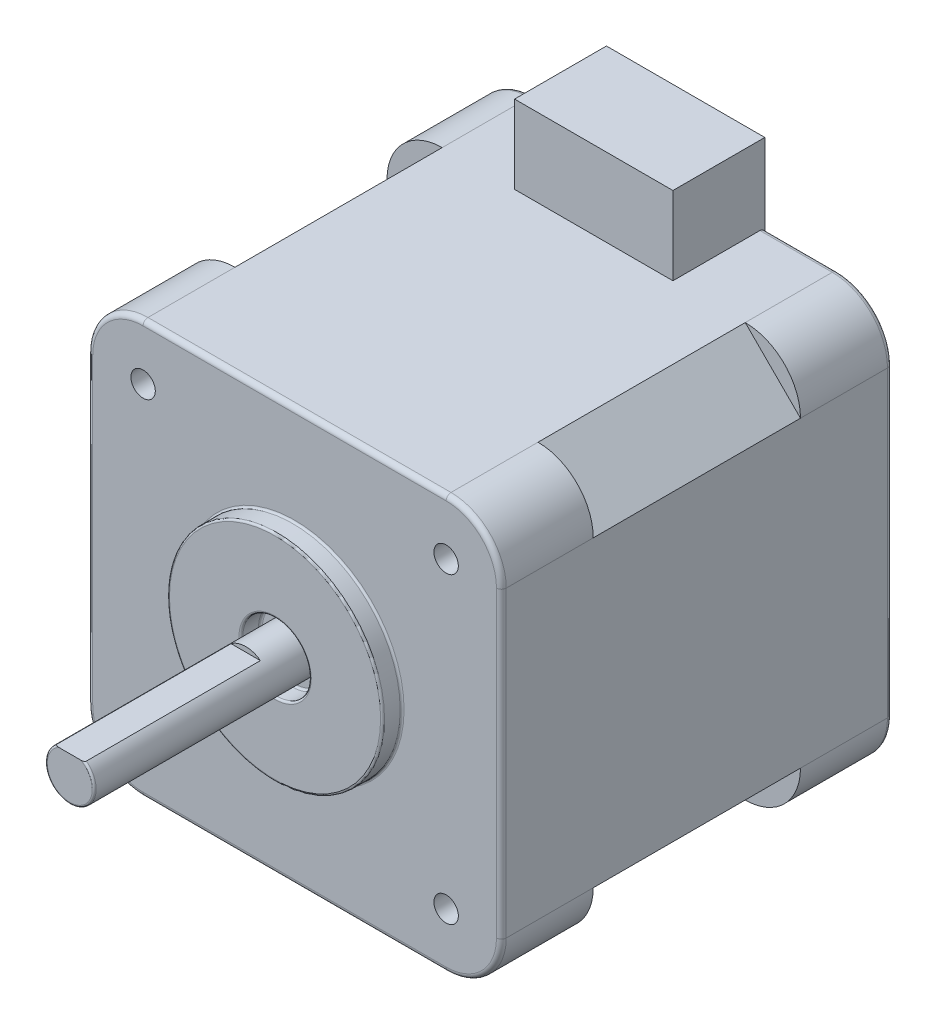
SolidWorks part; units mm, degrees
ref_plane "前视基准面" through (0, 0, 0) normal (0, 0, 1) x (1, 0, 0)
ref_plane "上视基准面" through (0, 0, 0) normal (0, 1, 0) x (1, 0, 0)
ref_plane "右视基准面" through (0, 0, 0) normal (1, 0, 0) x (0, 0, -1)
sketch "草图1" plane through (0, 0, 0) normal (0, 0, 1) x (1, 0, 0)
  line L1 (-21.15, -21.15) -> (21.15, -21.15)
  line L2 (-21.15, -21.15) -> (-21.15, 21.15)
  line L3 (-21.15, 21.15) -> (21.15, 21.15)
  line L4 (21.15, -21.15) -> (21.15, 21.15)
  line L5 (-21.15, -21.15) -> (21.15, 21.15) construction
  line L6 (-21.15, 21.15) -> (21.15, -21.15) construction
  point P0 (0, 0)
  dimension "D1" = 42.3
  dimension "D2" = 42.3
extrude "凸台-拉伸1" add sketch "草图1" along normal mid plane 21.2
chamfer "倒角1" distance 5.65 4 edges at (21.15, -21.15, 0) (-21.15, -21.15, 0) (-21.15, 21.15, 0) (21.15, 21.15, 0)
sketch "草图3" plane through (0, 0, 10.6) normal (0, 0, 1) x (1, 0, 0)
  line L0 (15.5, 21.15) -> (-15.5, 21.15) construction
  line L1 (21.15, -21.15) -> (-21.15, -21.15)
  line L2 (21.15, -21.15) -> (21.15, 21.15)
  line L3 (21.15, 21.15) -> (-21.15, 21.15)
  line L4 (-21.15, -21.15) -> (-21.15, 21.15)
  line L5 (21.15, -21.15) -> (-21.15, 21.15) construction
  line L6 (21.15, 21.15) -> (-21.15, -21.15) construction
  line L8 (-21.15, 15.5) -> (-21.15, -15.5) construction
  point P0 (0, 0)
extrude "凸台-拉伸2" add sketch "草图3" along normal blind 9.4
fillet "圆角1" radius 5.65 4 edges at (21.15, 21.15, 15.3) (21.15, -21.15, 15.3) (-21.15, -21.15, 15.3) (-21.15, 21.15, 15.3)
hole_wizard "M3 螺纹孔1" positions "草图4" profile "草图5" tap size "M3" standard "GB"
sketch "草图4" plane through (0, 0, 20) normal (0, 0, 1) x (1, 0, 0)
  point P0 (-15.5, -15.5)
  point P3 (15.5, -15.5)
  point P6 (15.5, 15.5)
  point P9 (-15.5, 15.5)
sketch "草图5" plane through (-15.5, -15.5, 20) normal (1, 0, 0) x (0, -1, 0)
  line L0 (0, 0) -> (0, 5.2511)
  line L1 (0, 5.2511) -> (1.25, 4.5)
  line L2 (1.25, 4.5) -> (1.25, 0)
  line L5 (1.25, 0) -> (0, 0)
  line L10 (0, 5.2511) -> (-1.25, 4.5) construction
  line L11 (0, -6.35) -> (0, 107.95) construction
  dimension "螺纹孔钻头直径" = 2.5
  dimension "螺纹孔钻头深度" = 4.5
  dimension "导头角度" = 118
cosmetic thread "孔螺蚊线1" parameters "D1"=4.5, "D2"=3
cosmetic thread "孔螺蚊线2" parameters "D1"=4.5, "D2"=3
cosmetic thread "孔螺蚊线3" parameters "D1"=4.5, "D2"=3
cosmetic thread "孔螺蚊线4" parameters "D1"=4.5, "D2"=3
sketch "草图6" plane through (0, 0, -10.6) normal (0, 0, -1) x (-1, 0, 0)
  line L1 (21.15, -21.15) -> (-21.15, -21.15)
  line L2 (21.15, -21.15) -> (21.15, 21.15)
  line L3 (21.15, 21.15) -> (-21.15, 21.15)
  line L4 (-21.15, -21.15) -> (-21.15, 21.15)
  line L5 (21.15, -21.15) -> (-21.15, 21.15) construction
  line L6 (21.15, 21.15) -> (-21.15, -21.15) construction
  line L7 (-15.5, 21.15) -> (15.5, 21.15) construction
  line L8 (-21.15, -15.5) -> (-21.15, 15.5) construction
  point P0 (0, 0)
extrude "凸台-拉伸3" add sketch "草图6" along normal blind 9.4
fillet "圆角2" radius 5.65 4 edges at (-21.15, -21.15, -15.3) (21.15, -21.15, -15.3) (21.15, 21.15, -15.3) (-21.15, 21.15, -15.3)
sketch "草图7" plane through (0, 21.15, 0) normal (0, 1, 0) x (1, 0, 0)
  line L0 (-15.5, 20) -> (15.5, 20) construction
  line L1 (8.1, 10.6) -> (-8.1, 10.6)
  line L2 (8.1, 10.6) -> (8.1, 20)
  line L3 (8.1, 20) -> (-8.1, 20)
  line L4 (-8.1, 10.6) -> (-8.1, 20)
  line L5 (8.1, 10.6) -> (-8.1, 20) construction
  line L6 (8.1, 20) -> (-8.1, 10.6) construction
  line L7 (15.5, 10.6) -> (21.15, 10.6) construction
  point P0 (0, 15.3)
  dimension "D1" = 16.2
extrude "凸台-拉伸4" add sketch "草图7" along normal blind 8
sketch "草图8" plane through (0, 0, 20) normal (0, 0, 1) x (1, 0, 0)
  circle A0 centre (0, 0) radius 11
  dimension "D1" = 22
extrude "凸台-拉伸5" add sketch "草图8" along normal blind 2
fillet "圆角3" radius 0.2 2 edges at (11, 0, 20) (11, 0, 22)
sketch "草图9" plane through (0, 0, 20) normal (0, 0, 1) x (1, 0, 0)
  circle A0 centre (0, 0) radius 3.5
  dimension "D1" = 7
extrude "切除-拉伸2" cut sketch "草图9" along normal up to next
fillet "圆角4" radius 0.2 2 edges at (3.5, 0, 22) (3.5, 0, 20)
sketch "草图11" plane through (0, 0, 20) normal (0, 0, 1) x (1, 0, 0)
  circle A0 centre (0, 0) radius 2.5
  dimension "D1" = 5
extrude "凸台-拉伸7" add sketch "草图11" along normal blind 23
fillet "圆角5" radius 0.2 1 edges at (2.5, 0, 43)
sketch "草图12" plane through (0, 0, 0) normal (1, 0, 0) x (0, 0, -1)
  line L0 (-20, 2.5) -> (-42.8, 2.5) construction
  line L1 (-25, 2) -> (-43, 2)
  line L2 (-25, 2) -> (-25, 2.5)
  line L3 (-25, 2.5) -> (-43, 2.5)
  line L4 (-43, 2) -> (-43, 2.5)
  line L6 (-43, 2.3) -> (-43, -2.3) construction
  line L7 (-42.8, -2.5) -> (-20, -2.5) construction
  dimension "D1" = 18
  dimension "D2" = 4.5
extrude "切除-拉伸3" cut sketch "草图12" against normal through all both and the other way through all
fillet "圆角6" radius 0.5 17 edges at (11.8, 21.15, -20) (19.4952, 19.4952, -20) (-11.8, 21.15, -20) (-19.4952, 19.4952, -20) (-21.15, 0, -20) (-19.4952, -19.4952, -20) (0, -21.15, -20) (19.4952, -19.4952, -20) (19.4952, 19.4952, 20) (21.15, 0, 20) (19.4952, -19.4952, 20) (0, -21.15, 20) (-19.4952, -19.4952, 20) (-21.15, 0, 20) (-19.4952, 19.4952, 20) (21.15, 0, -20) (0, 21.15, 20)
